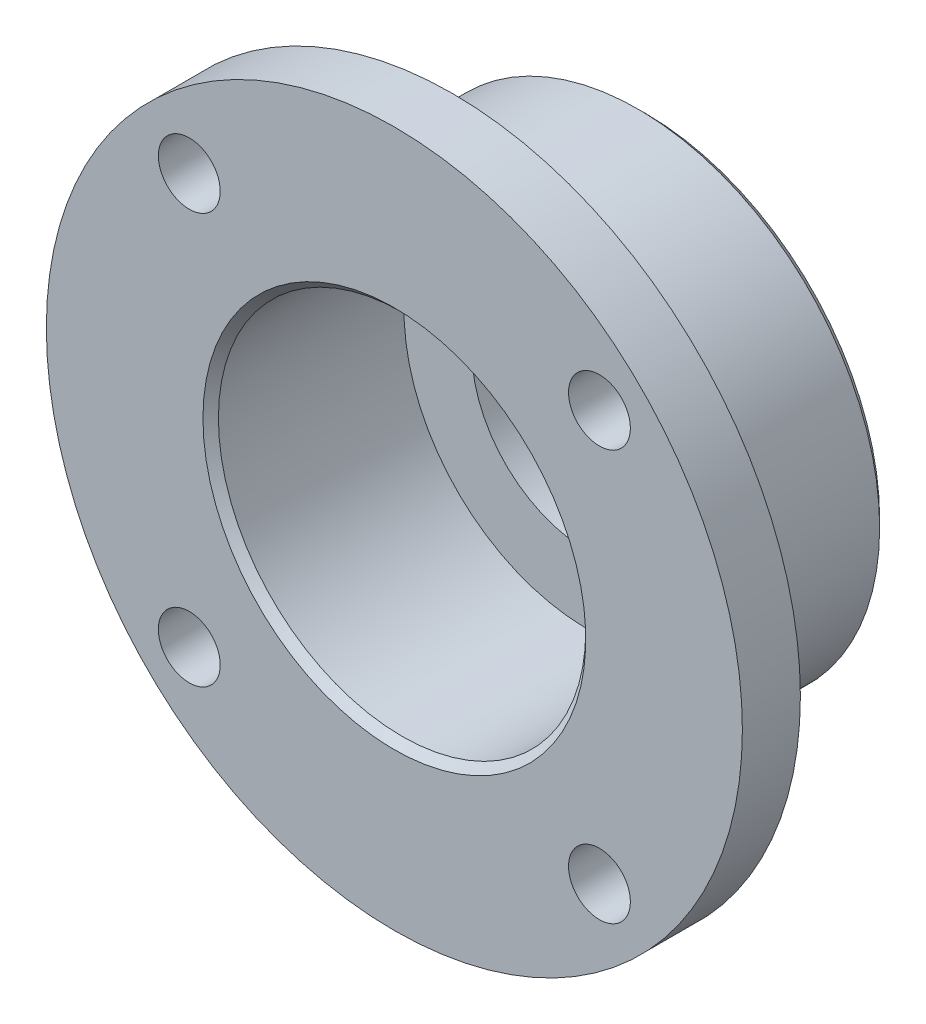
SolidWorks part; units mm, degrees
material "2024 Сплав"
ref_plane "Спереди" through (0, 0, 0) normal (0, 0, 1) x (1, 0, 0)
ref_plane "Сверху" through (0, 0, 0) normal (0, 1, 0) x (1, 0, 0)
ref_plane "Справа" through (0, 0, 0) normal (1, 0, 0) x (0, 0, -1)
sketch "Эскиз1" plane through (0, 0, 0) normal (0, 1, 0) x (1, 0, 0)
  line L0 (-18, 0) -> (-18, 3)
  line L1 (-18, 3) -> (-12.5, 3)
  line L2 (-12.5, 3) -> (-12.5, 13)
  line L3 (-12.5, 13) -> (-6, 13)
  line L4 (-6, 13) -> (-6, 10)
  line L6 (-9.5, 10) -> (-9.5, 0)
  line L7 (-9.5, 0) -> (-18, 0)
  line L8 (0, 0) -> (0, 50000) construction
  line L12 (-9.5, 10) -> (-6, 10)
  dimension "D1" = 6
  dimension "D2" = 12.5
  dimension "D3" = 9.5
  dimension "D4" = 3
  dimension "D5" = 3
  dimension "D6" = 18
  dimension "D7" = 13
revolve "Повернуть1" add sketch "Эскиз1" angle 360 about L8
sketch "Эскиз2" plane through (0, 0, 0) normal (0, 0, 1) x (1, 0, 0)
  line L0 (0, 0) -> (18, 0) construction
  circle A2 centre (0, 0) radius 9.5 construction
  circle A3 centre (10.6066, 10.6066) radius 1.6
  circle A4 centre (0, 0) radius 18 construction
  dimension "D1" = 15
  dimension "D2" = 3.2
  dimension "D3" = 45
extrude "Вырез-Вытянуть1" cut sketch "Эскиз2" against normal up to next (3 mm away)
pattern_circular "Круговой массив1" count 4 over 360 about axis through (0, 0, 0) along (0, 0, 1) of "Вырез-Вытянуть1"
chamfer "Фаска1" distance 0.4 angle 45 2 edges at (12.5, 0, -13) (9.5, 0, 0)
